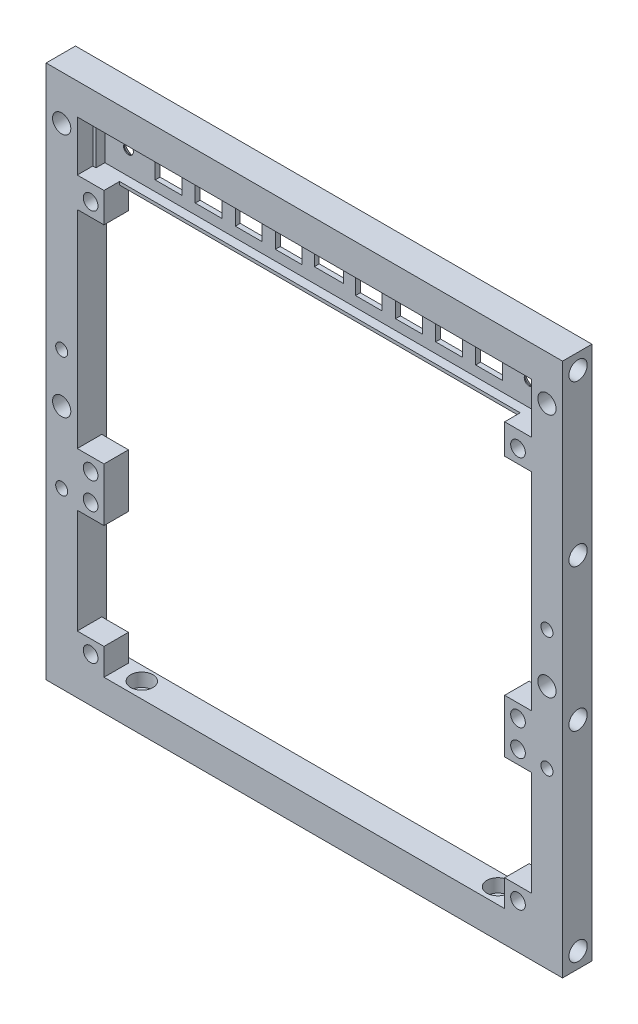
SolidWorks part; units mm, degrees
ref_plane "Front Plane" through (0, 0, 0) normal (0, 0, 1) x (1, 0, 0)
ref_plane "Top Plane" through (0, 0, 0) normal (0, 1, 0) x (1, 0, 0)
ref_plane "Right Plane" through (0, 0, 0) normal (1, 0, 0) x (0, 0, -1)
sketch "Sketch1" plane through (0, 0, 0) normal (0, 0, 1) x (1, 0, 0)
  line L1 (-58, -60) -> (58, -60)
  line L2 (-58, -60) -> (-58, 60)
  line L3 (-58, 60) -> (58, 60)
  line L4 (58, -60) -> (58, 60)
  line L5 (-58, -60) -> (58, 60) construction
  line L6 (-58, 60) -> (58, -60) construction
  line L7 (-51, -53) -> (51, -53)
  line L8 (-51, -53) -> (-51, 53)
  line L9 (-51, 53) -> (51, 53)
  line L10 (51, -53) -> (51, 53)
  line L11 (-51, -53) -> (51, 53) construction
  line L12 (-51, 53) -> (51, -53) construction
  point P0 (0, 0)
  point P6 (0, 0)
  dimension "D1" = 116
  dimension "D2" = 120
  dimension "D3" = 7
  dimension "D4" = 7
extrude "Boss-Extrude1" add sketch "Sketch1" along normal blind 7
sketch "Sketch2" plane through (-58, 0, 0) normal (-1, 0, 0) x (0, 0, 1)
  line L0 (3.5, 56.5) -> (3.5, -56.5) construction
  line L1 (7, 60) -> (0, 60) construction
  circle A0 centre (3.5, -56.5) radius 2.05
  circle A2 centre (3.5, 56.5) radius 2.05
  circle A3 centre (3.5, 20.5) radius 2.05
  circle A4 centre (3.5, -11.5) radius 2.05
  point P2 (3.5, 0)
  point P7 (3.5, 60)
  dimension "D2" = 4.1
  dimension "D3" = 36
  dimension "D4" = 45
  dimension "D1" = 3.5
extrude "Cut-Extrude1" cut sketch "Sketch2" against normal blind 6
mirror "Mirror1" about plane through (0, 0, 0) normal (1, 0, 0) of "Cut-Extrude1"
sketch "Sketch3" plane through (0, -53, 0) normal (0, 1, 0) x (1, 0, 0)
  line L0 (0, 0) -> (0, -7) construction
  line L1 (-51, 0) -> (51, 0) construction
  line L2 (-51, -7) -> (51, -7) construction
  line L3 (40, -3.5) -> (-40, -3.5) construction
  circle A0 centre (40, -3.5) radius 1.35
  circle A1 centre (-40, -3.5) radius 1.35
  point P9 (0, -3.5)
  dimension "D1" = 2.7
  dimension "D2" = 80
extrude "Cut-Extrude2" cut sketch "Sketch3" against normal through all
sketch "Sketch4" plane through (0, -53, 0) normal (0, 1, 0) x (1, 0, 0)
  circle A0 centre (40, -3.5) radius 2.5
  circle A1 centre (-40, -3.5) radius 2.5
  dimension "D1" = 5
extrude "Cut-Extrude3" cut sketch "Sketch4" against normal blind 3
sketch "Sketch5" plane through (0, 0, 0) normal (0, 0, -1) x (-1, 0, 0)
  line L0 (-54.5, -60) -> (-54.5, 60) construction
  line L1 (58, -60) -> (-58, -60) construction
  line L2 (-58, 60) -> (58, 60) construction
  line L3 (-51, 0) -> (-58, 0) construction
  line L4 (-51, -53) -> (-51, 53) construction
  line L5 (-58, -60) -> (-58, 60) construction
  line L6 (0, 60) -> (0, -60) construction
  line L7 (51, -53) -> (-51, -53) construction
  circle A0 centre (-54.5, 6) radius 1.35
  circle A1 centre (54.5, 6) radius 1.35
  circle A2 centre (-54.5, -21) radius 1.35
  circle A3 centre (54.5, -21) radius 1.35
  point P12 (-54.5, 0)
  point P13 (-54.5, 0)
  dimension "D1" = 2.7
  dimension "D2" = 6
  dimension "D3" = 32
extrude "Cut-Extrude4" cut sketch "Sketch5" against normal through all
sketch "Sketch6" plane through (0, 0, 0) normal (0, 0, -1) x (-1, 0, 0)
  circle A0 centre (-54.5, 6) radius 2.5
  circle A1 centre (54.5, 6) radius 2.5
  circle A2 centre (-54.5, -21) radius 2.5
  circle A3 centre (54.5, -21) radius 2.5
  dimension "D1" = 5
extrude "Cut-Extrude5" cut sketch "Sketch6" against normal blind 3
sketch "Sketch7" plane through (0, 0, 0) normal (0, 0, -1) x (-1, 0, 0)
  line L0 (-51, 53) -> (-58, 53) construction
  line L1 (-58, -60) -> (-58, 60) construction
  line L2 (-54.5, 50) -> (-54.5, -5) construction
  line L3 (-58, 60) -> (58, 60) construction
  circle A0 centre (-54.5, 50) radius 2.05
  circle A1 centre (-54.5, -5) radius 2.05
  point P8 (-54.5, 53)
  dimension "D1" = 4.1
  dimension "D2" = 10
  dimension "D3" = 55
extrude "Cut-Extrude6" cut sketch "Sketch7" against normal through all
mirror "Mirror2" about plane through (0, 0, 0) normal (1, 0, 0) of "Cut-Extrude6"
sketch "Sketch8" plane through (0, 0, 3) normal (0, 0, -1) x (-1, 0, 0)
  line L2 (-55.85, 3.8958) -> (-55.85, 8.1042)
  line L4 (-53.15, 3.8958) -> (-53.15, 8.1042)
  line L5 (-55.85, 3.8958) -> (-53.15, 8.1042) construction
  line L6 (-55.85, 8.1042) -> (-53.15, 3.8958) construction
  line L8 (-55.85, -23.1042) -> (-55.85, -18.8958)
  line L10 (-53.15, -23.1042) -> (-53.15, -18.8958)
  line L11 (-55.85, -23.1042) -> (-53.15, -18.8958) construction
  line L12 (-55.85, -18.8958) -> (-53.15, -23.1042) construction
  circle A0 centre (-54.5, 6) radius 2.5 construction
  circle A1 centre (-54.5, -21) radius 2.5 construction
  circle A2 centre (-54.5, -21) radius 2.5 construction
  arc A3 (-53.15, 8.1042) -> (-55.85, 8.1042) centre (-54.5, 6) ccw
  arc A4 (-53.15, -18.8958) -> (-55.85, -18.8958) centre (-54.5, -21) ccw
  circle A5 centre (-54.5, 6) radius 1.35 construction
  circle A6 centre (-54.5, -21) radius 1.35 construction
  arc A7 (-55.85, -23.1042) -> (-53.15, -23.1042) centre (-54.5, -21) ccw
  arc A8 (-55.85, 3.8958) -> (-53.15, 3.8958) centre (-54.5, 6) ccw
  point P0 (-54.5, 6)
  point P8 (-54.5, -21)
extrude "Cut-Extrude7" cut sketch "Sketch8" against normal blind 0.2
sketch "Sketch9" plane through (0, 0, 3.2) normal (0, 0, -1) x (-1, 0, 0)
  line L0 (-53.15, 6) -> (-53.15, 8.1042) construction
  line L1 (-55.85, 4.65) -> (-53.15, 4.65)
  line L2 (-55.85, 4.65) -> (-55.85, 7.35)
  line L3 (-55.85, 7.35) -> (-53.15, 7.35)
  line L4 (-53.15, 4.65) -> (-53.15, 7.35)
  line L5 (-55.85, 4.65) -> (-53.15, 7.35) construction
  line L6 (-55.85, 7.35) -> (-53.15, 4.65) construction
  line L7 (-53.15, -23.1042) -> (-53.15, -18.8958) construction
  line L8 (-55.85, -22.35) -> (-53.15, -22.35)
  line L9 (-55.85, -22.35) -> (-55.85, -19.65)
  line L10 (-55.85, -19.65) -> (-53.15, -19.65)
  line L11 (-53.15, -22.35) -> (-53.15, -19.65)
  line L12 (-55.85, -22.35) -> (-53.15, -19.65) construction
  line L13 (-55.85, -19.65) -> (-53.15, -22.35) construction
  arc A0 (-53.15, 6) -> (-55.85, 6) centre (-54.5, 6) ccw construction
  point P0 (-54.5, 6)
  point P8 (-54.5, -21)
extrude "Cut-Extrude8" cut sketch "Sketch9" against normal blind 0.2
mirror "Mirror3" about plane through (0, 0, 0) normal (1, 0, 0) of "Cut-Extrude8", "Cut-Extrude7"
sketch "Sketch10" plane through (0, 0, 7) normal (0, 0, 1) x (1, 0, 0)
  line L0 (51, -53) -> (51, 53) construction
  line L1 (51, -53) -> (45, -53)
  line L2 (51, -53) -> (51, -47)
  line L3 (51, -47) -> (45, -47)
  line L4 (45, -53) -> (45, -47)
  line L5 (51, -23.5) -> (45, -23.5)
  line L6 (51, -23.5) -> (51, -17.5)
  line L7 (51, -17.5) -> (45, -17.5)
  line L8 (45, -23.5) -> (45, -17.5)
  line L9 (-51, -53) -> (51, -53) construction
  dimension "D1" = 6
  dimension "D2" = 35.5
extrude "Boss-Extrude2" add sketch "Sketch10" against normal offset from surface (5.5 mm away) 1.5 up to face at (-52.45, -5, 0)
sketch "Sketch11" plane through (0, 0, 1.5) normal (0, 0, -1) x (-1, 0, 0)
  line L0 (-51, -23.5) -> (-45, -17.5) construction
  line L2 (-51, -53) -> (-45, -47) construction
  circle A0 centre (-48, -20.5) radius 1.65
  circle A1 centre (-48, -50) radius 1.65
  dimension "D1" = 3.3
extrude "Cut-Extrude9" cut sketch "Sketch11" against normal through all
mirror "Mirror4" about plane through (0, 0, 0) normal (1, 0, 0) of "Cut-Extrude9", "Boss-Extrude2"
sketch "Sketch12" plane through (0, 0, 0) normal (0, 0, -1) x (-1, 0, 0)
  line L0 (51, 53) -> (51, -53) construction
  line L1 (-51, 53) -> (51, 53)
  line L2 (-51, 53) -> (-51, 41)
  line L3 (-51, 41) -> (51, 41)
  line L4 (51, 53) -> (51, 41)
  dimension "D1" = 12
extrude "Boss-Extrude3" add sketch "Sketch12" against normal blind 1.5
sketch "Sketch13" plane through (0, 0, 1.5) normal (0, 0, 1) x (1, 0, 0)
  line L0 (-51, 53) -> (51, 41) construction
  line L2 (-50.3, 41.7) -> (50.3, 41.7)
  line L3 (-50.3, 41.7) -> (-50.3, 52.3)
  line L4 (-50.3, 52.3) -> (50.3, 52.3)
  line L5 (50.3, 41.7) -> (50.3, 52.3)
  line L6 (-50.3, 41.7) -> (50.3, 52.3) construction
  line L7 (-50.3, 52.3) -> (50.3, 41.7) construction
  line L8 (-51, 41) -> (51, 41)
  line L9 (-51, 41) -> (-51, 53)
  line L10 (-51, 53) -> (51, 53)
  line L11 (51, 41) -> (51, 53)
  line L12 (-51, 41) -> (51, 53) construction
  line L13 (-51, 53) -> (51, 41) construction
  point P4 (0, 47)
  point P9 (0, 47)
  dimension "D1" = 100.6
  dimension "D2" = 10.6
extrude "Boss-Extrude4" add sketch "Sketch13" along normal blind 2
sketch "Sketch14" plane through (0, 0, 1.5) normal (0, 0, 1) x (1, 0, 0)
  line L0 (0, 52.3) -> (0, 41.7) construction
  line L1 (50.3, 52.3) -> (-50.3, 52.3) construction
  line L2 (-50.3, 41.7) -> (50.3, 41.7) construction
  line L3 (-50.3, 47) -> (50.3, 47) construction
  line L4 (50.3, 41.7) -> (50.3, 52.3) construction
  line L5 (-33, 50) -> (-39, 50)
  line L6 (-3.25, 45) -> (3.25, 45)
  line L7 (-3.25, 45) -> (-3.25, 49)
  line L8 (-3.25, 49) -> (3.25, 49)
  line L9 (3.25, 45) -> (3.25, 49)
  line L10 (-3.25, 45) -> (3.25, 49) construction
  line L11 (-3.25, 49) -> (3.25, 45) construction
  line L12 (6, 44) -> (12, 44)
  line L13 (6, 44) -> (6, 50)
  line L14 (6, 50) -> (12, 50)
  line L15 (12, 44) -> (12, 50)
  line L16 (6, 44) -> (12, 50) construction
  line L17 (6, 50) -> (12, 44) construction
  line L18 (15, 44) -> (21, 44)
  line L19 (15, 44) -> (15, 50)
  line L20 (15, 50) -> (21, 50)
  line L21 (21, 44) -> (21, 50)
  line L22 (15, 44) -> (21, 50) construction
  line L23 (15, 50) -> (21, 44) construction
  line L24 (24, 44) -> (30, 44)
  line L25 (24, 44) -> (24, 50)
  line L26 (24, 50) -> (30, 50)
  line L27 (30, 44) -> (30, 50)
  line L28 (24, 44) -> (30, 50) construction
  line L29 (24, 50) -> (30, 44) construction
  line L30 (33, 44) -> (39, 44)
  line L31 (33, 44) -> (33, 50)
  line L32 (33, 50) -> (39, 50)
  line L33 (39, 44) -> (39, 50)
  line L34 (33, 44) -> (39, 50) construction
  line L35 (33, 50) -> (39, 44) construction
  line L36 (-39, 44) -> (-39, 50)
  line L37 (-33, 44) -> (-39, 44)
  line L38 (-33, 44) -> (-33, 50)
  line L39 (-24, 50) -> (-30, 50)
  line L40 (-30, 44) -> (-30, 50)
  line L41 (-24, 44) -> (-30, 44)
  line L42 (-24, 44) -> (-24, 50)
  line L43 (-15, 50) -> (-21, 50)
  line L44 (-21, 44) -> (-21, 50)
  line L45 (-15, 44) -> (-21, 44)
  line L46 (-15, 44) -> (-15, 50)
  line L47 (-6, 50) -> (-12, 50)
  line L48 (-12, 44) -> (-12, 50)
  line L49 (-6, 44) -> (-12, 44)
  line L50 (-6, 44) -> (-6, 50)
  circle A0 centre (-45, 47) radius 1.3 construction
  circle A1 centre (45, 47) radius 1.3 construction
  point P6 (0, 47)
  point P11 (0, 47)
  point P16 (9, 47)
  point P21 (18, 47)
  point P26 (27, 47)
  point P31 (36, 47)
  dimension "D10" = 2.6
  dimension "D9" = 45
  dimension "D1" = 6.5
  dimension "D2" = 4
  dimension "D3" = 6
  dimension "D4" = 9
  dimension "D5" = 9
  dimension "D6" = 9
  dimension "D7" = 9
  dimension "D8" = 45
extrude "Cut-Extrude10" cut sketch "Sketch14" against normal through all
sketch "Sketch15" plane through (0, 0, 1.5) normal (0, 0, 1) x (1, 0, 0)
  circle A0 centre (-45, 47) radius 1
  circle A1 centre (45, 47) radius 1
  dimension "D1" = 2
extrude "Boss-Extrude5" add sketch "Sketch15" along normal up to surface (2 mm away) up to face at (0, 47, 3.5)
chamfer "Chamfer1" distance 0.4 angle 45 4 edges at (-51, -6, 0) (51, -6, 0) (0, -53, 0) (0, 41, 0)
chamfer "Chamfer2" distance 0.4 angle 45 4 edges at (0, 60, 0) (-58, 0, 0) (0, -60, 0) (58, 0, 0)
chamfer "Chamfer3" distance 0.4 angle 45 36 edges at (-36, 44, 0) (-39, 47, 0) (-36, 50, 0) (-33, 47, 0) (-27, 44, 0) (-30, 47, 0) (-27, 50, 0) (-24, 47, 0) (-18, 44, 0) (-21, 47, 0) (-18, 50, 0) (-15, 47, 0) (-9, 44, 0) (-12, 47, 0) (-9, 50, 0) (-6, 47, 0) (0, 45, 0) (-3.25, 47, 0) (0, 49, 0) (3.25, 47, 0) (9, 44, 0) (6, 47, 0) (9, 50, 0) (12, 47, 0) (18, 44, 0) (15, 47, 0) (18, 50, 0) (21, 47, 0) (36, 44, 0) (33, 47, 0) (36, 50, 0) (39, 47, 0) (27, 44, 0) (24, 47, 0) (27, 50, 0) (30, 47, 0)
sketch "Sketch16" plane through (0, 0, 7) normal (0, 0, 1) x (1, 0, 0)
  line L0 (-45, 41) -> (-45, 41.7)
  line L1 (-51, -17.5) -> (-45, -17.5)
  line L2 (-51, -17.5) -> (-51, -11.5)
  line L3 (-51, -11.5) -> (-45, -11.5)
  line L4 (-45, -17.5) -> (-45, -11.5)
  line L5 (51, -17.5) -> (45, -17.5)
  line L6 (51, -17.5) -> (51, -11.5)
  line L7 (51, -11.5) -> (45, -11.5)
  line L8 (45, -17.5) -> (45, -11.5)
  line L9 (51, 41) -> (45, 41) construction
  line L10 (51, 41) -> (51, 35)
  line L11 (51, 35) -> (45, 35)
  line L12 (45, 41) -> (45, 35)
  line L13 (-51, 41) -> (-45, 41) construction
  line L14 (-51, 41) -> (-51, 35)
  line L15 (-51, 35) -> (-45, 35)
  line L16 (-45, 41) -> (-45, 35)
  line L17 (-50.3, 41.7) -> (50.3, 41.7) construction
  line L18 (-45, 41.7) -> (-51, 41.7)
  line L19 (-51, 53) -> (-51, 41) construction
  line L20 (-51, 41.7) -> (-51, 41)
  line L21 (45, 41) -> (45, 41.7)
  line L22 (45, 41.7) -> (51, 41.7)
  line L23 (51, 41) -> (51, 53) construction
  line L24 (51, 41.7) -> (51, 41)
  dimension "D1" = 6
extrude "Boss-Extrude7" add sketch "Sketch16" against normal offset from surface (5.5 mm away) 1.5 up to face at (-36, 47, 0)
sketch "Sketch17" plane through (0, 0, 1.5) normal (0, 0, -1) x (-1, 0, 0)
  line L0 (-45, 35) -> (45, -11.5) construction
  line L1 (-45, -11.5) -> (-45, -23.5) construction
  line L2 (-48, -14.5) -> (48, -14.5) construction
  line L3 (-48, -14.5) -> (-48, 38) construction
  line L4 (-48, 38) -> (48, 38) construction
  line L5 (48, -14.5) -> (48, 38) construction
  line L6 (-48, -14.5) -> (48, 38) construction
  line L7 (-48, 38) -> (48, -14.5) construction
  line L8 (45, -11.5) -> (51, -11.5) construction
  circle A0 centre (-48, -14.5) radius 1.65
  circle A1 centre (48, -14.5) radius 1.65
  circle A2 centre (48, 38) radius 1.65
  circle A3 centre (-48, 38) radius 1.65
  point P4 (0, 11.75)
  dimension "D3" = 3.3
  dimension "D1" = 3
  dimension "D2" = 3
extrude "Cut-Extrude11" cut sketch "Sketch17" against normal through all
sketch "Sketch18" plane through (0, 0, 1.5) normal (0, 0, 1) x (1, 0, 0)
  circle A0 centre (-45, 47) radius 1.1
  circle A1 centre (45, 47) radius 1.1
  dimension "D1" = 2.2
extrude "Cut-Extrude12" cut sketch "Sketch18" against normal through all both and the other way through all
chamfer "Chamfer4" distance 1.3 angle 45 2 edges at (-43.9, 47, 0) (46.1, 47, 0)
